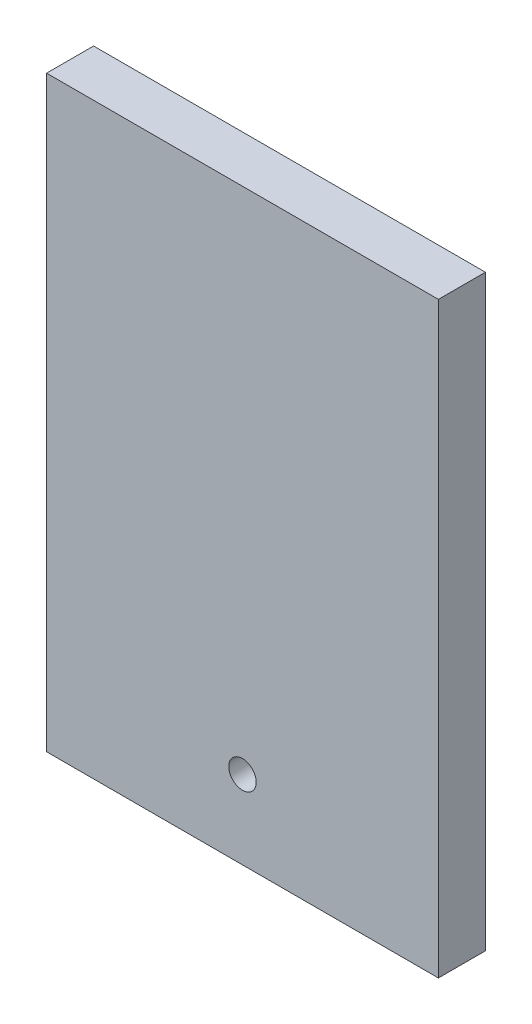
SolidWorks part; units mm, degrees
ref_plane "Front Plane" through (0, 0, 0) normal (0, 0, 1) x (1, 0, 0)
ref_plane "Top Plane" through (0, 0, 0) normal (0, 1, 0) x (1, 0, 0)
ref_plane "Right Plane" through (0, 0, 0) normal (1, 0, 0) x (0, 0, -1)
sketch "Sketch1" plane through (0, 0, 0) normal (0, 0, 1) x (1, 0, 0)
  line L1 (0, 0) -> (50.8, 0)
  line L2 (0, 0) -> (0, 76.2)
  line L3 (0, 76.2) -> (50.8, 76.2)
  line L4 (50.8, 0) -> (50.8, 76.2)
  dimension "D1" = 76.2
  dimension "D2" = 50.8
extrude "Boss-Extrude1" add sketch "Sketch1" along normal blind 6.096
sketch "Sketch2" plane through (0, 0, 0) normal (0, 0, -1) x (-1, 0, 0)
  circle A0 centre (-25.4, 10.16) radius 1.778 construction
  circle A1 centre (-25.4, 10.16) radius 1.778
extrude "Cut-Extrude1" cut sketch "Sketch2" against normal through all
equation "\"mat\" = \"mat@fsc.assembly\""
equation "\"D1@Boss-Extrude1\"= \"mat\""
